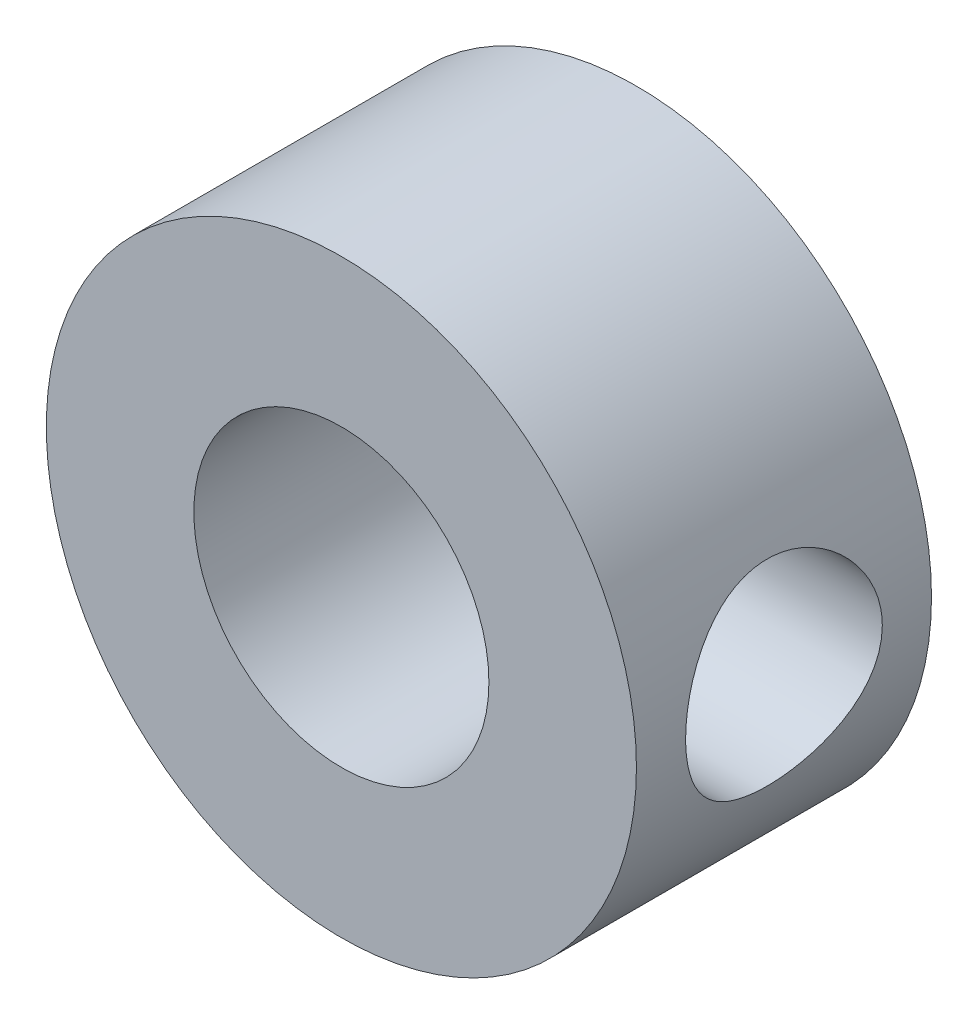
SolidWorks part; units mm, degrees
ref_plane "Front Plane" through (0, 0, 0) normal (0, 0, 1) x (1, 0, 0)
ref_plane "Top Plane" through (0, 0, 0) normal (0, 1, 0) x (1, 0, 0)
ref_plane "Right Plane" through (0, 0, 0) normal (1, 0, 0) x (0, 0, -1)
sketch "Sketch1" plane through (0, 0, 0) normal (0, 0, 1) x (1, 0, 0)
  circle A0 centre (-356.05, 162.7) radius 9.525
  circle A1 centre (-356.05, 162.7) radius 4.7625
  dimension "D1" = 19.05
  dimension "D2" = 9.525
extrude "Extrude1" add sketch "Sketch1" along normal mid plane 9.525
sketch "Sketch2" plane through (0, 0, 0) normal (1, 0, 0) x (0, 0, -1)
  line L0 (4.7625, 172.225) -> (-4.7625, 153.175) construction
  line L1 (-4.7625, 153.175) -> (4.7625, 153.175) construction
  line L2 (-4.7625, 172.225) -> (-4.7625, 153.175) construction
  circle A0 centre (0, 162.7) radius 3.175
  dimension "D1" = 6.35
extrude "Cut-Extrude1" cut sketch "Sketch2" against normal blind 354.5533
